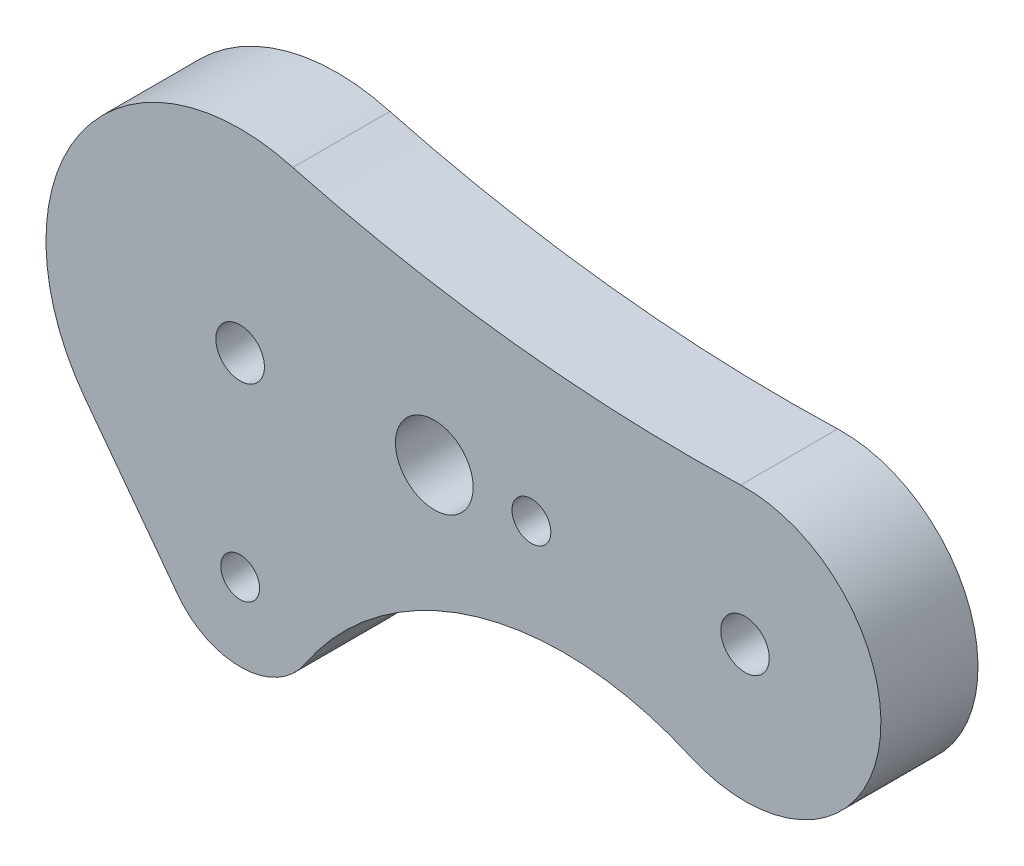
SolidWorks part; units mm, degrees
material "PMMA"
ref_plane "Front Plane" through (0, 0, 0) normal (0, 0, 1) x (1, 0, 0)
ref_plane "Top Plane" through (0, 0, 0) normal (0, 1, 0) x (1, 0, 0)
ref_plane "Right Plane" through (0, 0, 0) normal (1, 0, 0) x (0, 0, -1)
sketch "Sketch1" plane through (0, 0, 0) normal (0, 0, 1) x (1, 0, 0)
  line L0 (0, 0) -> (26, 0) construction
  line L1 (0, 0) -> (0, -10) construction
  line L2 (-8, -6) -> (-3.2, -12.4)
  circle A0 centre (0, 0) radius 1.25
  circle A1 centre (26, 0) radius 1.25
  circle A2 centre (10, 0) radius 2
  circle A3 centre (15, 0) radius 1
  circle A4 centre (0, -10) radius 1
  arc A5 (-3.2, -12.4) -> (3.3368, -12.2058) centre (0, -10) ccw
  arc A6 (23.1648, -6.4001) -> (25.7753, 6.9964) centre (26, 0) ccw
  arc A8 (2.7129, 9.625) -> (25.7753, 6.9964) centre (23.2078, 86.9552) ccw
  arc A9 (3.3368, -12.2058) -> (23.1648, -6.4001) centre (16.6842, -21.0289) cw
  arc A10 (2.7129, 9.625) -> (-8, -6) centre (0, 0) ccw
  dimension "D1" = 2.5
  dimension "D2" = 2.5
  dimension "D4" = 4
  dimension "D6" = 2
  dimension "D10" = 2
  dimension "D8" = 14
  dimension "D11" = 10
  dimension "D12" = 4
  dimension "D13" = 80
  dimension "D14" = 16
  dimension "D3" = 26
  dimension "D5" = 10
  dimension "D7" = 11
  dimension "D9" = 10
  dimension "D15" = 2.7129
  dimension "D16" = 8
extrude "Boss-Extrude1" add sketch "Sketch1" along normal blind 5
cosmetic thread "Cosmetic Thread1" parameters "D2"=2.5
cosmetic thread "Cosmetic Thread2" parameters "D2"=3
